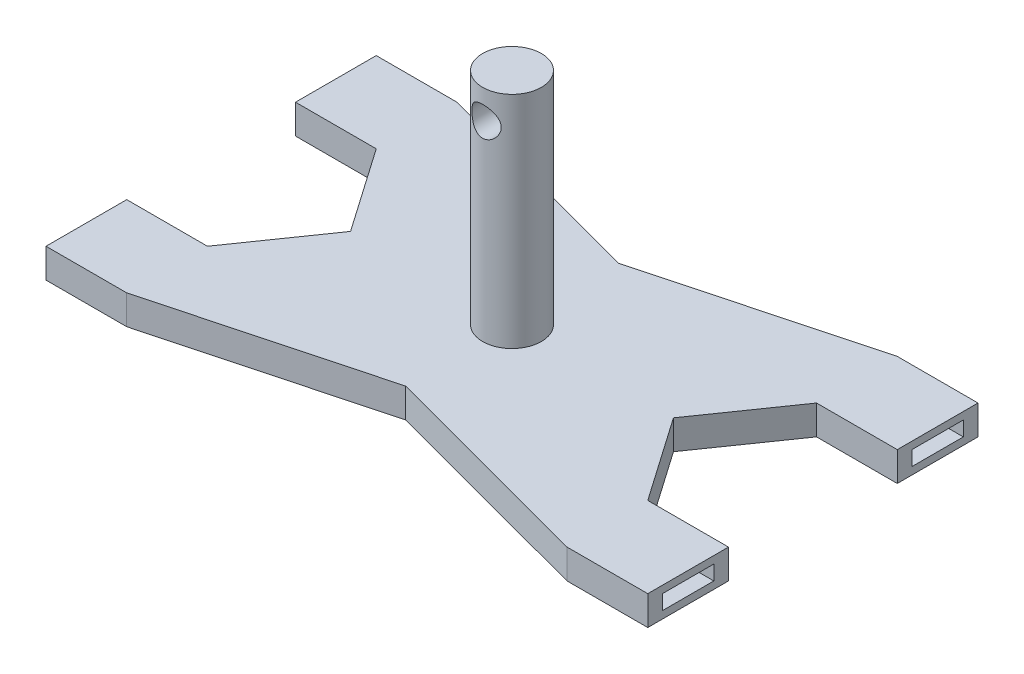
SolidWorks part; units mm, degrees
ref_plane "Alzado" through (0, 0, 0) normal (0, 0, 1) x (1, 0, 0)
ref_plane "Planta" through (0, 0, 0) normal (0, 1, 0) x (1, 0, 0)
ref_plane "Vista lateral" through (0, 0, 0) normal (1, 0, 0) x (0, 0, -1)
sketch "Croquis1" plane through (0, 0, 0) normal (0, 1, 0) x (1, 0, 0)
  line L0 (-41, -22.5) -> (-30, -22.5)
  line L1 (-30, -22.5) -> (30, -22.5) construction
  line L2 (30, -22.5) -> (30, -11.5) construction
  line L3 (-30, 22.5) -> (30, 22.5) construction
  line L4 (30, 11.5) -> (30, 22.5) construction
  line L5 (-30, -22.5) -> (30, 22.5) construction
  line L6 (30, -22.5) -> (-30, 22.5) construction
  line L7 (30, -22.5) -> (41, -22.5)
  line L8 (41, -22.5) -> (41, -11.5)
  line L9 (41, -11.5) -> (30, -11.5)
  line L10 (30, -11.5) -> (30, 11.5) construction
  line L11 (30, 11.5) -> (41, 11.5)
  line L12 (41, 11.5) -> (41, 22.5)
  line L13 (41, 22.5) -> (30, 22.5)
  line L14 (30, -22.5) -> (0, -14.5)
  line L15 (0, -14.5) -> (-30, -22.5)
  line L16 (-30, 22.5) -> (-41, 22.5)
  line L17 (-41, 22.5) -> (-41, 11.5)
  line L18 (-41, 11.5) -> (-30, 11.5)
  line L19 (-30, 11.5) -> (-30, -11.5) construction
  line L20 (-30, -11.5) -> (-41, -11.5)
  line L21 (-41, -11.5) -> (-41, -22.5)
  line L22 (-30, -11.5) -> (-22, 0)
  line L23 (-22, 0) -> (-30, 11.5)
  line L24 (-30, 11.5) -> (-30, 22.5) construction
  line L25 (-30, -22.5) -> (-30, -11.5) construction
  line L26 (-30, 22.5) -> (0, 14.5)
  line L27 (0, 14.5) -> (30, 22.5)
  line L28 (30, 11.5) -> (22, 0)
  line L29 (22, 0) -> (30, -11.5)
  point P0 (0, 0)
  point P1 (0, 0)
  dimension "D6" = 45
  dimension "D1" = 60
  dimension "D2" = 23
  dimension "D3" = 11
  dimension "D4" = 11
  dimension "D5" = 8
  dimension "D7" = 8
extrude "Saliente-Extruir1" add sketch "Croquis1" along normal blind 4
sketch "Croquis4" plane through (-41, 0, 0) normal (-1, 0, 0) x (0, 0, 1)
  line L0 (-22.5, 2) -> (-11.5, 2) construction
  line L2 (-20.5, 3) -> (-13.5, 3)
  line L3 (-20.5, 3) -> (-20.5, 1)
  line L4 (-20.5, 1) -> (-13.5, 1)
  line L5 (-22.5, 4) -> (-22.5, 0) construction
  line L6 (-11.5, 4) -> (-11.5, 0) construction
  line L7 (-17, 4) -> (-17, 0) construction
  line L8 (-22.5, 4) -> (-11.5, 4) construction
  line L9 (-22.5, 0) -> (-11.5, 0) construction
  line L10 (-13.5, 3) -> (-13.5, 1)
  line L11 (-20.5, 3) -> (-13.5, 1) construction
  line L12 (-20.5, 1) -> (-13.5, 3) construction
  point P0 (-17, 2)
  dimension "D1" = 7
  dimension "D2" = 2
extrude "Cortar-Extruir2" cut sketch "Croquis4" against normal blind 9
sketch "Croquis6" plane through (-41, 0, 0) normal (-1, 0, 0) x (0, 0, 1)
  line L0 (17, 4) -> (17, 0) construction
  line L1 (11.5, 4) -> (22.5, 4) construction
  line L2 (11.5, 0) -> (22.5, 0) construction
  line L3 (22.5, 4) -> (22.5, 0) construction
  line L4 (11.5, 4) -> (11.5, 0) construction
  line L5 (11.5, 2) -> (22.5, 2) construction
  line L7 (13.5, 3) -> (20.5, 3)
  line L8 (13.5, 3) -> (13.5, 1)
  line L9 (13.5, 1) -> (20.5, 1)
  line L10 (20.5, 3) -> (20.5, 1)
  line L11 (13.5, 3) -> (20.5, 1) construction
  line L12 (13.5, 1) -> (20.5, 3) construction
  point P6 (17, 2)
  dimension "D1" = 7
  dimension "D2" = 2
sketch "Croquis7" plane through (41, 0, 0) normal (1, 0, 0) x (0, 0, -1)
  line L0 (-17, 0) -> (-17, 4) construction
  line L1 (-22.5, 0) -> (-11.5, 0) construction
  line L2 (-22.5, 4) -> (-11.5, 4) construction
  line L4 (-22.5, 4) -> (-22.5, 0) construction
  line L5 (-22.5, 2) -> (-11.5, 2) construction
  line L6 (-11.5, 4) -> (-11.5, 0) construction
  line L7 (-20.5, 1) -> (-13.5, 1)
  line L8 (-20.5, 1) -> (-20.5, 3)
  line L9 (-20.5, 3) -> (-13.5, 3)
  line L10 (-13.5, 1) -> (-13.5, 3)
  line L11 (-20.5, 1) -> (-13.5, 3) construction
  line L12 (-20.5, 3) -> (-13.5, 1) construction
  point P6 (-17, 2)
  dimension "D1" = 7
  dimension "D2" = 2
extrude "Cortar-Extruir6" cut sketch "Croquis6" against normal blind 9
extrude "Cortar-Extruir4" cut sketch "Croquis7" against normal blind 9
sketch "Croquis8" plane through (41, 0, 0) normal (1, 0, 0) x (0, 0, -1)
  line L0 (17, 4) -> (17, 0) construction
  line L1 (11.5, 4) -> (22.5, 4) construction
  line L2 (11.5, 0) -> (22.5, 0) construction
  line L4 (11.5, 4) -> (11.5, 0) construction
  line L5 (11.5, 2) -> (22.5, 2) construction
  line L6 (22.5, 4) -> (22.5, 0) construction
  line L7 (13.5, 1) -> (20.5, 1)
  line L8 (13.5, 1) -> (13.5, 3)
  line L9 (13.5, 3) -> (20.5, 3)
  line L10 (20.5, 1) -> (20.5, 3)
  line L11 (13.5, 1) -> (20.5, 3) construction
  line L12 (13.5, 3) -> (20.5, 1) construction
  point P6 (17, 2)
  dimension "D1" = 7
  dimension "D2" = 2
extrude "Cortar-Extruir5" cut sketch "Croquis8" against normal blind 9
sketch "Croquis9" plane through (0, 4, 0) normal (0, 1, 0) x (1, 0, 0)
  circle A0 centre (0, 0) radius 4
  dimension "D1" = 8
extrude "Saliente-Extruir2" add sketch "Croquis9" along normal blind 30
sketch "Croquis10" plane through (0, 0, 0) normal (0, 0, 1) x (1, 0, 0)
  line L0 (0, 0) -> (0, 30) construction
  circle A0 centre (0, 30) radius 2
  dimension "D1" = 4
  dimension "D2" = 30
extrude "Cortar-Extruir7" cut sketch "Croquis10" against normal through all and the other way through all
